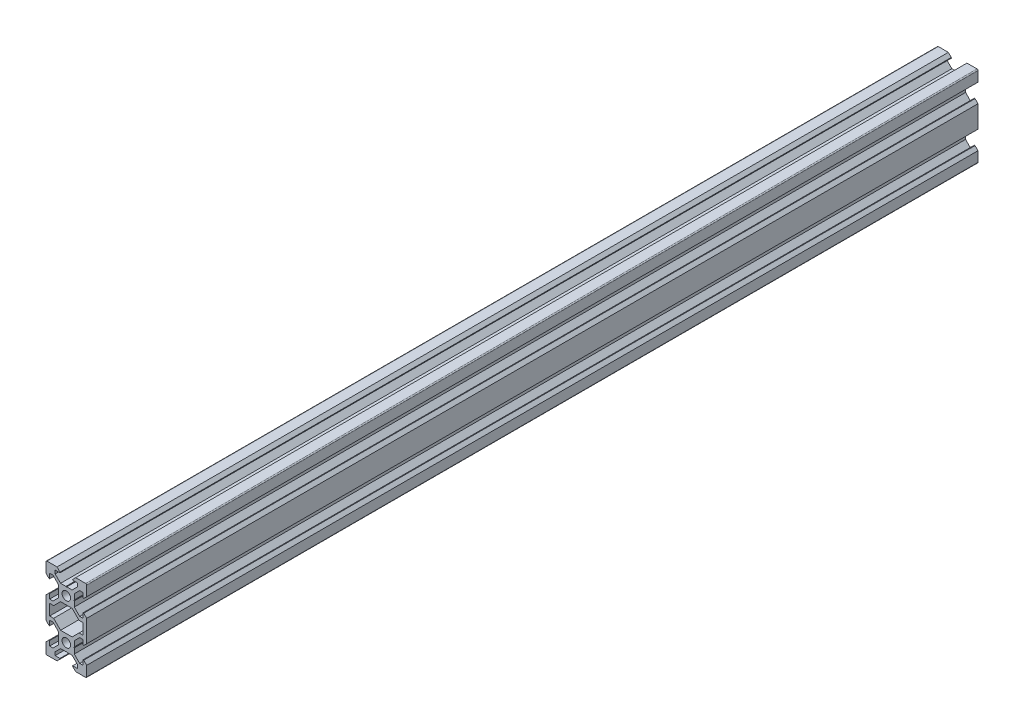
SolidWorks part; units mm, degrees
material "6061-T6 (SS)"
ref_plane "Front Plane" through (0, 0, 0) normal (0, 0, 1) x (1, 0, 0)
ref_plane "Top Plane" through (0, 0, 0) normal (0, 1, 0) x (1, 0, 0)
ref_plane "Right Plane" through (0, 0, 0) normal (1, 0, 0) x (0, 0, -1)
sketch "Sketch1" plane through (0, 0, 0) normal (0, 0, 1) x (1, 0, 0)
  line L0 (0, 0) -> (10, 0) construction
  line L1 (9.5, -20) -> (-9.5, -20)
  line L2 (10, -19.5) -> (10, 19.5)
  line L3 (9.5, 20) -> (-9.5, 20)
  line L4 (-10, -19.5) -> (-10, 19.5)
  line L5 (10, -20) -> (-10, 20) construction
  line L6 (10, 20) -> (-10, -20) construction
  circle A0 centre (0, 10) radius 2.1
  circle A1 centre (0, -10) radius 2.1
  arc A2 (-9.5, -20) -> (-10, -19.5) centre (-9.5, -19.5) cw
  arc A3 (9.5, -20) -> (10, -19.5) centre (9.5, -19.5) ccw
  arc A4 (10, 19.5) -> (9.5, 20) centre (9.5, 19.5) ccw
  arc A5 (-9.5, 20) -> (-10, 19.5) centre (-9.5, 19.5) ccw
  point P0 (0, 0)
  line B0 (0, 10) -> (0, 20) construction
  line B1 (0, 13.69) -> (-0.21, 13.9)
  line B2 (-0.21, 13.9) -> (-2.8393, 13.9)
  line B3 (-2.8393, 13.9) -> (-5.5, 16.5607)
  line B4 (-5.5, 16.5607) -> (-5.5, 18.2)
  line B5 (-5.5, 18.2) -> (-3.125, 18.2)
  line B6 (-3.125, 18.2) -> (-3.125, 18.545)
  line B7 (-3.125, 18.545) -> (-4.58, 20)
  line B8 (-4.58, 20) -> (4.58, 20)
  line B9 (0, 10) -> (-5.9132, 15.9132) construction
  line B10 (3.125, 18.545) -> (4.58, 20)
  line B11 (3.125, 18.2) -> (3.125, 18.545)
  line B12 (5.5, 18.2) -> (3.125, 18.2)
  line B13 (5.5, 16.5607) -> (5.5, 18.2)
  line B14 (2.8393, 13.9) -> (5.5, 16.5607)
  line B15 (0.21, 13.9) -> (2.8393, 13.9)
  line B16 (0, 13.69) -> (0.21, 13.9)
  line B17 (0, 10) -> (-10, 10) construction
  line B18 (-3.69, 10) -> (-3.9, 9.79)
  line B19 (-3.9, 9.79) -> (-3.9, 7.1607)
  line B20 (-3.9, 7.1607) -> (-6.5607, 4.5)
  line B21 (-6.5607, 4.5) -> (-8.2, 4.5)
  line B22 (-8.2, 4.5) -> (-8.2, 6.875)
  line B23 (-8.2, 6.875) -> (-8.545, 6.875)
  line B24 (-8.545, 6.875) -> (-10, 5.42)
  line B25 (-10, 5.42) -> (-10, 14.58)
  line B26 (0, 10) -> (-5.9132, 4.0868) construction
  line B27 (-8.545, 13.125) -> (-10, 14.58)
  line B28 (-8.2, 13.125) -> (-8.545, 13.125)
  line B29 (-8.2, 15.5) -> (-8.2, 13.125)
  line B30 (-6.5607, 15.5) -> (-8.2, 15.5)
  line B31 (-3.9, 12.8393) -> (-6.5607, 15.5)
  line B32 (-3.9, 10.21) -> (-3.9, 12.8393)
  line B33 (-3.69, 10) -> (-3.9, 10.21)
  line B34 (0, -10) -> (-10, -10) construction
  line B35 (-3.69, -10) -> (-3.9, -10.21)
  line B36 (-3.9, -10.21) -> (-3.9, -12.8393)
  line B37 (-3.9, -12.8393) -> (-6.5607, -15.5)
  line B38 (-6.5607, -15.5) -> (-8.2, -15.5)
  line B39 (-8.2, -15.5) -> (-8.2, -13.125)
  line B40 (-8.2, -13.125) -> (-8.545, -13.125)
  line B41 (-8.545, -13.125) -> (-10, -14.58)
  line B42 (-10, -14.58) -> (-10, -5.42)
  line B43 (0, -10) -> (-5.9132, -15.9132) construction
  line B44 (-8.545, -6.875) -> (-10, -5.42)
  line B45 (-8.2, -6.875) -> (-8.545, -6.875)
  line B46 (-8.2, -4.5) -> (-8.2, -6.875)
  line B47 (-6.5607, -4.5) -> (-8.2, -4.5)
  line B48 (-3.9, -7.1607) -> (-6.5607, -4.5)
  line B49 (-3.9, -9.79) -> (-3.9, -7.1607)
  line B50 (-3.69, -10) -> (-3.9, -9.79)
  line B51 (0, -10) -> (0, -20) construction
  line B52 (0, -13.69) -> (0.21, -13.9)
  line B53 (0.21, -13.9) -> (2.8393, -13.9)
  line B54 (2.8393, -13.9) -> (5.5, -16.5607)
  line B55 (5.5, -16.5607) -> (5.5, -18.2)
  line B56 (5.5, -18.2) -> (3.125, -18.2)
  line B57 (3.125, -18.2) -> (3.125, -18.545)
  line B58 (3.125, -18.545) -> (4.58, -20)
  line B59 (4.58, -20) -> (-4.58, -20)
  line B60 (0, -10) -> (5.9132, -15.9132) construction
  line B61 (-3.125, -18.545) -> (-4.58, -20)
  line B62 (-3.125, -18.2) -> (-3.125, -18.545)
  line B63 (-5.5, -18.2) -> (-3.125, -18.2)
  line B64 (-5.5, -16.5607) -> (-5.5, -18.2)
  line B65 (-2.8393, -13.9) -> (-5.5, -16.5607)
  line B66 (-0.21, -13.9) -> (-2.8393, -13.9)
  line B67 (0, -13.69) -> (-0.21, -13.9)
  line B68 (0, -10) -> (10, -10) construction
  line B69 (3.69, -10) -> (3.9, -9.79)
  line B70 (3.9, -9.79) -> (3.9, -7.1607)
  line B71 (3.9, -7.1607) -> (6.5607, -4.5)
  line B72 (6.5607, -4.5) -> (8.2, -4.5)
  line B73 (8.2, -4.5) -> (8.2, -6.875)
  line B74 (8.2, -6.875) -> (8.545, -6.875)
  line B75 (8.545, -6.875) -> (10, -5.42)
  line B76 (10, -5.42) -> (10, -14.58)
  line B77 (0, -10) -> (5.9132, -4.0868) construction
  line B78 (8.545, -13.125) -> (10, -14.58)
  line B79 (8.2, -13.125) -> (8.545, -13.125)
  line B80 (8.2, -15.5) -> (8.2, -13.125)
  line B81 (6.5607, -15.5) -> (8.2, -15.5)
  line B82 (3.9, -12.8393) -> (6.5607, -15.5)
  line B83 (3.9, -10.21) -> (3.9, -12.8393)
  line B84 (3.69, -10) -> (3.9, -10.21)
  line B85 (0, 10) -> (10, 10) construction
  line B86 (3.69, 10) -> (3.9, 10.21)
  line B87 (3.9, 10.21) -> (3.9, 12.8393)
  line B88 (3.9, 12.8393) -> (6.5607, 15.5)
  line B89 (6.5607, 15.5) -> (8.2, 15.5)
  line B90 (8.2, 15.5) -> (8.2, 13.125)
  line B91 (8.2, 13.125) -> (8.545, 13.125)
  line B92 (8.545, 13.125) -> (10, 14.58)
  line B93 (10, 14.58) -> (10, 5.42)
  line B94 (0, 10) -> (5.9132, 15.9132) construction
  line B95 (8.545, 6.875) -> (10, 5.42)
  line B96 (8.2, 6.875) -> (8.545, 6.875)
  line B97 (8.2, 4.5) -> (8.2, 6.875)
  line B98 (6.5607, 4.5) -> (8.2, 4.5)
  line B99 (3.9, 7.1607) -> (6.5607, 4.5)
  line B100 (3.9, 9.79) -> (3.9, 7.1607)
  line B101 (3.69, 10) -> (3.9, 9.79)
  line B102 (-8.2, -2.7) -> (-8.2, 2.7)
  line B103 (-8.2, 2.7) -> (-6.2393, 2.7)
  line B104 (-6.2393, 2.7) -> (-2.8393, 6.1)
  line B105 (-2.8393, 6.1) -> (2.8393, 6.1)
  line B106 (0, 6.1) -> (0, 0) construction
  line B107 (0, 0) -> (-8.2, 0) construction
  line B108 (6.2393, 2.7) -> (2.8393, 6.1)
  line B109 (8.2, 2.7) -> (6.2393, 2.7)
  line B110 (8.2, -2.7) -> (8.2, 2.7)
  line B111 (8.2, -2.7) -> (6.2393, -2.7)
  line B112 (6.2393, -2.7) -> (2.8393, -6.1)
  line B113 (-2.8393, -6.1) -> (2.8393, -6.1)
  line B114 (-6.2393, -2.7) -> (-2.8393, -6.1)
  line B115 (-8.2, -2.7) -> (-6.2393, -2.7)
  line B116 (0, 6.1) -> (0, 10) construction
  line B117 (0, 10) -> (-5.0927, 4.9073) construction
  dimension "D4" = 4.2
  dimension "D5" = 0.5
  dimension "D1" = 20
  dimension "D2" = 40
  dimension "D3" = 20
sketch_block_instance "V Slot 1-4"
sketch_block "V Slot 1" parameters "D1"=10, "D2"=11, "D3"=4.3, "D4"=1.8, "D5"=0.21, "D6"=45, "D7"=9.16, "D8"=1.5, "D9"=6.25
sketch_block_instance "V Slot 1-5"
sketch_block_instance "V Slot 1-6"
sketch_block_instance "V Slot 1-7"
sketch_block_instance "V Slot 1-8"
sketch_block_instance "V Slot 1-9"
sketch_block_instance "Center Cutout 1-1"
sketch_block "Center Cutout 1" parameters "D1"=5.4, "D2"=12.2, "D3"=8.2, "D4"=45, "D5"=10, "D6"=1.5
extrude "Boss-Extrude1" add sketch "Sketch1" along normal blind 438 contours B101 B86 B87 B88 B89 B90 B91 B92 L2 A4 L3 B10 B11 B12 B13 B14 B15 B16 B1 B2 B3 B4 B5 B6 B7 A5 L4 B27 B28 B29 B30 B31 B32 B33 B18 B19 B20 B21 B22 B23 B24 B44 B45 B46 B47 B48 B49 B50 B35
